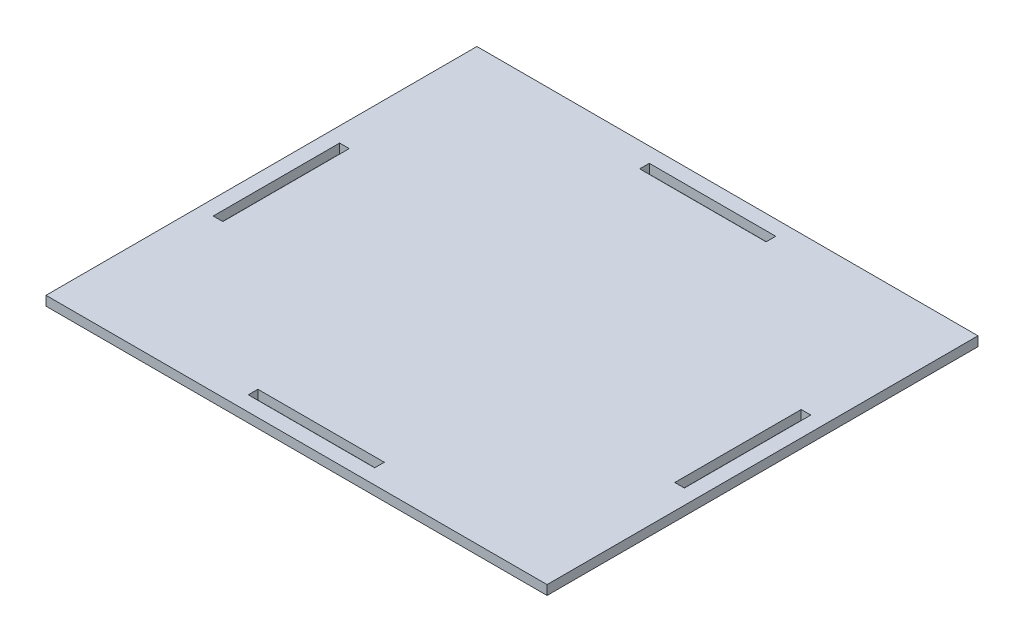
SolidWorks part; units mm, degrees
ref_plane "Front Plane" through (0, 0, 0) normal (0, 0, 1) x (1, 0, 0)
ref_plane "Top Plane" through (0, 0, 0) normal (0, 1, 0) x (1, 0, 0)
ref_plane "Right Plane" through (0, 0, 0) normal (1, 0, 0) x (0, 0, -1)
sketch "Sketch1" plane through (0, 0, 0) normal (0, 1, 0) x (1, 0, 0)
  line L1 (-79.375, -68.2625) -> (79.375, -68.2625)
  line L2 (-79.375, -68.2625) -> (-79.375, 68.2625)
  line L3 (-79.375, 68.2625) -> (79.375, 68.2625)
  line L4 (79.375, -68.2625) -> (79.375, 68.2625)
  line L5 (-79.375, -68.2625) -> (79.375, 68.2625) construction
  line L6 (-79.375, 68.2625) -> (79.375, -68.2625) construction
  point P0 (0, 0)
  dimension "D1" = 136.525
  dimension "D2" = 158.75
extrude "Boss-Extrude1" add sketch "Sketch1" along normal mid plane 2.9972
sketch "Sketch2" plane through (0, 1.4986, 0) normal (0, 1, 0) x (1, 0, 0)
  line L0 (0, 68.2625) -> (0, 0) construction
  line L1 (-20.0254, 63.5254) -> (20.0254, 63.5254)
  line L2 (-20.0254, 63.5254) -> (-20.0254, 60.4774)
  line L3 (-20.0254, 60.4774) -> (20.0254, 60.4774)
  line L4 (20.0254, 63.5254) -> (20.0254, 60.4774)
  line L5 (-74.6379, 20.0254) -> (-71.5899, 20.0254)
  line L6 (-74.6379, 20.0254) -> (-74.6379, -20.0254)
  line L7 (-74.6379, -20.0254) -> (-71.5899, -20.0254)
  line L8 (-71.5899, 20.0254) -> (-71.5899, -20.0254)
  line L9 (79.375, 68.2625) -> (-79.375, 68.2625) construction
  line L10 (0, 0) -> (-79.375, 0) construction
  line L11 (-79.375, 68.2625) -> (-79.375, -68.2625) construction
  line L12 (20.0254, -63.5254) -> (20.0254, -60.4774)
  line L13 (-20.0254, -60.4774) -> (20.0254, -60.4774)
  line L14 (-20.0254, -63.5254) -> (-20.0254, -60.4774)
  line L15 (-20.0254, -63.5254) -> (20.0254, -63.5254)
  line L16 (71.5899, 20.0254) -> (71.5899, -20.0254)
  line L17 (74.6379, -20.0254) -> (71.5899, -20.0254)
  line L18 (74.6379, 20.0254) -> (74.6379, -20.0254)
  line L19 (74.6379, 20.0254) -> (71.5899, 20.0254)
  point P13 (-71.5899, 0)
  point P17 (0, 60.4774)
  dimension "D1" = 3.048
  dimension "D2" = 3.048
  dimension "D3" = 40.0508
  dimension "D4" = 40.0508
  dimension "D5" = 149.2758
  dimension "D6" = 127.0508
extrude "Cut-Extrude1" cut sketch "Sketch2" against normal through all
